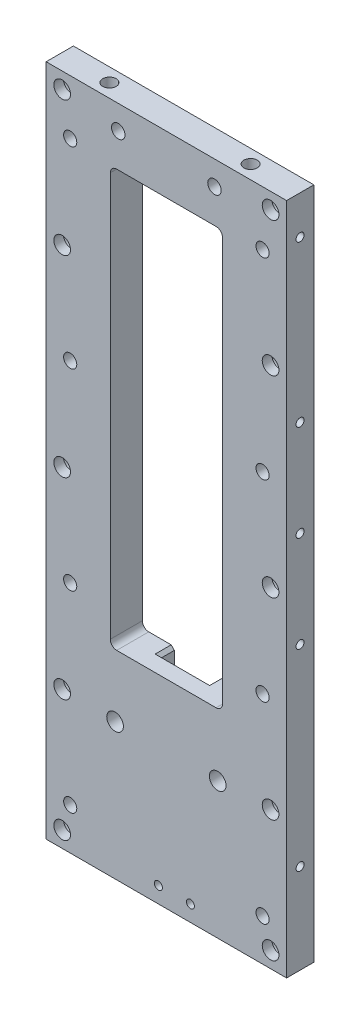
SolidWorks part; units mm, degrees
ref_plane "Front Plane" through (0, 0, 0) normal (0, 0, 1) x (1, 0, 0)
ref_plane "Top Plane" through (0, 0, 0) normal (0, 1, 0) x (1, 0, 0)
ref_plane "Right Plane" through (0, 0, 0) normal (1, 0, 0) x (0, 0, -1)
sketch "Sketch1" plane through (0, 0, 0) normal (0, 0, 1) x (1, 0, 0)
  line L0 (0, 0) -> (0, 230.9156) construction
  line L1 (0, 0) -> (0, -61.2047) construction
  line L2 (-37.5, 0) -> (0, 0)
  line L3 (0, 0) -> (37.5, 0)
  line L4 (-37.5, 210) -> (0, 210)
  line L5 (0, 210) -> (37.5, 210)
  line L6 (37.5, 210) -> (37.5, 0)
  line L7 (-37.5, 210) -> (-37.5, 0)
  point P8 (0, 230.9156)
  point P10 (0, 0)
  point P11 (0, 0)
  dimension "D1" = 75
  dimension "D2" = 210
extrude "Boss-Extrude1" add sketch "Sketch1" along normal blind 10
sketch "Sketch2" plane through (0, 0, 0) normal (0, 0, -1) x (-1, 0, 0)
  line L0 (0, 0) -> (0, 210) construction
  line L1 (-37.5, 210) -> (37.5, 210) construction
  line L2 (-30, 210) -> (-30, 0) construction
  line L3 (37.5, 0) -> (-37.5, 0) construction
  line L4 (-30, 193) -> (-18.2699, 193) construction
  line L5 (-30, 133) -> (-18.2699, 133) construction
  line L6 (-30, 73) -> (-18.2699, 73) construction
  line L7 (-30, 13) -> (-18.2699, 13) construction
  line L8 (-37.5, 0) -> (-37.5, 210) construction
  point P17 (0, 0)
  point P18 (0, 0)
  point P19 (0, 0)
  point P20 (0, 0)
  point P21 (30, 13)
  point P22 (30, 73)
  point P23 (30, 133)
  point P24 (30, 193)
  dimension "D1" = 30
  dimension "D2" = 60
  dimension "D3" = 60
  dimension "D4" = 60
  dimension "D5" = 17
hole_wizard "M5 Tapped Hole1" positions "3DSketch1" profile "Sketch3" tap size "M5" standard "GB"
sketch3d "3DSketch1"
  point P0 (30, 193, 0)
  point P3 (30, 133, 0)
  point P6 (30, 73, 0)
  point P9 (30, 13, 0)
  point P12 (-30, 13, 0)
  point P15 (-30, 73, 0)
  point P18 (-30, 133, 0)
  point P21 (-30, 193, 0)
sketch "Sketch3" plane through (30, 193, 0) normal (1, 0, 0) x (0, 1, 0)
  line L0 (0, 0) -> (0, 15.2318)
  line L1 (0, 15.2318) -> (2.05, 14)
  line L2 (2.05, 14) -> (2.05, 0)
  line L5 (2.05, 0) -> (0, 0)
  line L10 (0, 15.2318) -> (-2.05, 14) construction
  line L11 (0, -6.35) -> (0, 107.95) construction
  dimension "Tap Drill Dia." = 4.1
  dimension "Tap Drill Depth" = 14
  dimension "Drill Angle" = 118
cosmetic thread "Hole Thread1" parameters "D1"=10, "D2"=5
cosmetic thread "Hole Thread2" parameters "D1"=10, "D2"=5
cosmetic thread "Hole Thread3" parameters "D1"=10, "D2"=5
cosmetic thread "Hole Thread4" parameters "D1"=10, "D2"=5
cosmetic thread "Hole Thread5" parameters "D1"=10, "D2"=5
cosmetic thread "Hole Thread6" parameters "D1"=10, "D2"=5
cosmetic thread "Hole Thread7" parameters "D1"=10, "D2"=5
cosmetic thread "Hole Thread8" parameters "D1"=10, "D2"=5
sketch "Sketch4" plane through (0, 0, 0) normal (0, 0, -1) x (-1, 0, 0)
  line L0 (0, 0) -> (0, 210) construction
  line L1 (-37.5, 210) -> (37.5, 210) construction
  line L3 (17.5, 62) -> (-17.5, 62)
  line L4 (17.5, 62) -> (17.5, 192)
  line L5 (17.5, 192) -> (-17.5, 192)
  line L6 (-17.5, 62) -> (-17.5, 192)
  line L7 (17.5, 62) -> (-17.5, 192) construction
  line L8 (17.5, 192) -> (-17.5, 62) construction
  point P5 (0, 127)
  dimension "D1" = 127
  dimension "D2" = 130
  dimension "D3" = 35
extrude "Cut-Extrude1" cut sketch "Sketch4" against normal up to next
fillet "Fillet1" radius 2 4 edges at (17.5, 62, 5) (-17.5, 62, 5) (17.5, 192, 5) (-17.5, 192, 5)
sketch "Sketch6" plane through (0, 0, 0) normal (0, 0, -1) x (-1, 0, 0)
  line L0 (0, 0) -> (0, 210) construction
  line L1 (-37.5, 210) -> (37.5, 210) construction
  line L2 (-37.5, 210) -> (-37.5, 0)
  line L3 (-37.5, 0) -> (-22.5, 0)
  line L4 (37.5, 0) -> (-37.5, 0) construction
  line L5 (-22.5, 0) -> (-22.5, 210)
  line L6 (-22.5, 210) -> (-37.5, 210)
  line L7 (22.5, 0) -> (22.5, 210)
  line L8 (37.5, 0) -> (22.5, 0)
  line L9 (37.5, 210) -> (37.5, 0)
  line L10 (22.5, 210) -> (37.5, 210)
  dimension "D1" = 15
extrude "Cut-Extrude2" cut sketch "Sketch6" against normal blind 1.5
sketch "Sketch7" plane through (0, 0, 0) normal (0, 0, -1) x (-1, 0, 0)
  line L0 (-22.5, 210) -> (-22.5, 195)
  line L1 (-22.5, 0) -> (-22.5, 210) construction
  line L2 (-22.5, 195) -> (22.5, 195)
  line L3 (22.5, 210) -> (22.5, 0) construction
  line L4 (22.5, 195) -> (22.5, 210)
  line L5 (22.5, 210) -> (-22.5, 210)
  line L6 (15.5, 192) -> (-15.5, 192) construction
  dimension "D1" = 3
extrude "Cut-Extrude3" cut sketch "Sketch7" against normal blind 1.5
sketch "Sketch8" plane through (0, 0, 1.5) normal (0, 0, -1) x (-1, 0, 0)
  line L0 (0, 0) -> (0, 268.5028) construction
  line L1 (-32.5, 210) -> (-32.5, 0) construction
  line L2 (37.5, 210) -> (-37.5, 210) construction
  line L3 (-37.5, 0) -> (-22.5, 0) construction
  line L4 (-37.5, 210) -> (-37.5, 0) construction
  line L5 (-32.5, 205) -> (-27.8232, 205) construction
  line L6 (-32.5, 163) -> (-27.2642, 163) construction
  line L7 (-32.5, 103) -> (-27.2642, 103) construction
  line L8 (-32.5, 43) -> (-25.9311, 43) construction
  line L9 (-32.5, 5) -> (-27.2642, 5) construction
  point P24 (32.5, 5)
  point P25 (32.5, 43)
  point P26 (32.5, 103)
  point P27 (32.5, 163)
  point P28 (32.5, 205)
  dimension "D1" = 5
  dimension "D2" = 5
  dimension "D3" = 30
  dimension "D4" = 30
  dimension "D5" = 30
  dimension "D6" = 5
hole_wizard "CBORE for M5 Hex Socket Head Cap Screw1" positions "3DSketch2" profile "Sketch9" counterbore size "M5" standard "ISO" end condition through all
sketch3d "3DSketch2"
  point P0 (32.5, 205, 1.5)
  point P3 (32.5, 163, 1.5)
  point P6 (32.5, 103, 1.5)
  point P9 (32.5, 43, 1.5)
  point P12 (32.5, 5, 1.5)
  point P15 (-32.5, 5, 1.5)
  point P18 (-32.5, 43, 1.5)
  point P21 (-32.5, 103, 1.5)
  point P24 (-32.5, 163, 1.5)
  point P27 (-32.5, 205, 1.5)
sketch "Sketch9" plane through (32.5, 205, 1.5) normal (1, 0, 0) x (0, 1, 0)
  line L0 (0, 0) -> (0, 8.5)
  line L1 (0, 8.5) -> (2.6, 8.5)
  line L3 (2.6, 8.5) -> (2.6, 5.5)
  line L4 (2.6, 5.5) -> (4.25, 5.5)
  line L5 (4.25, 5.5) -> (4.25, 0)
  line L7 (4.25, 0) -> (0, 0)
  line L11 (0, -6.35) -> (0, 107.95) construction
  dimension "Thru Hole Dia." = 5.2
  dimension "Thru Hole Depth" = 8.5
  dimension "C'Bore Dia." = 8.5
  dimension "C'Bore Depth" = 5.5
sketch "Sketch10" plane through (0, 210, 0) normal (0, 1, 0) x (1, 0, 0)
  line L0 (0, 0) -> (0, -10) construction
  line L1 (37.5, -10) -> (-37.5, -10) construction
  line L4 (-22, -5.75) -> (-22, -10) construction
  point P5 (22, -5.75)
  dimension "D1" = 22
  dimension "D2" = 4.25
hole_wizard "M5 Tapped Hole2" positions "3DSketch3" profile "Sketch11" tap size "M5" standard "GB"
sketch3d "3DSketch3"
  point P0 (-22, 210, 5.75)
  point P3 (22, 210, 5.75)
sketch "Sketch11" plane through (-22, 210, 5.75) normal (1, 0, 0) x (0, 0, 1)
  line L0 (0, 0) -> (0, 17.2618)
  line L1 (0, 17.2618) -> (2.1, 16)
  line L2 (2.1, 16) -> (2.1, 0)
  line L5 (2.1, 0) -> (0, 0)
  line L10 (0, 17.2618) -> (-2.1, 16) construction
  line L11 (0, -6.35) -> (0, 107.95) construction
  dimension "Tap Drill Dia." = 4.2
  dimension "Tap Drill Depth" = 16
  dimension "Drill Angle" = 118
cosmetic thread "Hole Thread9" parameters "D1"=12, "D2"=5
cosmetic thread "Hole Thread10" parameters "D1"=12, "D2"=5
sketch "Sketch12" plane through (0, 0, 1.5) normal (0, 0, -1) x (-1, 0, 0)
  line L0 (0, 0) -> (0, 210) construction
  line L1 (37.5, 210) -> (-37.5, 210) construction
  line L2 (-18.6459, 202.5) -> (-15, 202.5) construction
  line L3 (-15, 207.873) -> (-15, 202.5) construction
  line L4 (-22.5, 195) -> (22.5, 195) construction
  point P10 (15, 202.5)
  dimension "D1" = 15
  dimension "D2" = 7.5
hole_wizard "M5 Tapped Hole3" positions "3DSketch4" profile "Sketch13" tap size "M5" standard "GB"
sketch3d "3DSketch4"
  point P0 (15, 202.5, 1.5)
  point P3 (-15, 202.5, 1.5)
sketch "Sketch13" plane through (15, 202.5, 1.5) normal (1, 0, 0) x (0, 1, 0)
  line L0 (0, 0) -> (0, 104.8218)
  line L1 (0, 104.8218) -> (2.1, 103.56)
  line L2 (2.1, 103.56) -> (2.1, 0)
  line L5 (2.1, 0) -> (0, 0)
  line L10 (0, 104.8218) -> (-2.1, 103.56) construction
  line L11 (0, -6.35) -> (0, 107.95) construction
  dimension "Tap Drill Dia." = 4.2
  dimension "Tap Drill Depth" = 103.56
  dimension "Drill Angle" = 118
cosmetic thread "Hole Thread11" parameters "D1"=8.5, "D2"=5
cosmetic thread "Hole Thread12" parameters "D1"=8.5, "D2"=5
sketch "Sketch14" plane through (0, 0, 0) normal (0, 0, -1) x (-1, 0, 0)
  line L0 (-22.5, 53) -> (22.5, 53)
  line L1 (-22.5, 0) -> (-22.5, 195) construction
  line L2 (22.5, 195) -> (22.5, 0) construction
  line L3 (22.5, 53) -> (22.5, 35)
  line L4 (22.5, 195) -> (22.5, 0) construction
  line L5 (22.5, 35) -> (-22.5, 35)
  line L6 (-22.5, 35) -> (-22.5, 53)
  line L7 (-15.5, 62) -> (15.5, 62) construction
  dimension "D1" = 27
  dimension "D2" = 18
extrude "Cut-Extrude4" cut sketch "Sketch14" against normal blind 5
fillet "Fillet2" radius 2 4 edges at (-22.5, 35, 3.25) (22.5, 35, 3.25) (-22.5, 53, 3.25) (22.5, 53, 3.25)
sketch "Sketch15" plane through (0, 0, 0) normal (0, 0, -1) x (-1, 0, 0)
  line L0 (0, 0) -> (0, 78.6156) construction
  line L1 (-15.5, 62) -> (15.5, 62) construction
  line L2 (-7.5, 53) -> (7.5, 53)
  line L3 (-7.5, 53) -> (-7.5, 71)
  line L4 (-7.5, 71) -> (7.5, 71)
  line L5 (7.5, 53) -> (7.5, 71)
  line L6 (-7.5, 53) -> (7.5, 71) construction
  line L7 (-7.5, 71) -> (7.5, 53) construction
  line L8 (20.5, 53) -> (-20.5, 53) construction
  point P3 (0, 62)
  point P10 (0, 0)
  dimension "D1" = 15
extrude "Cut-Extrude6" cut sketch "Sketch15" against normal up to surface (5 mm away) up to face at (0, 44, 5)
sketch "Sketch16" plane through (0, 0, 5) normal (0, 0, -1) x (-1, 0, 0)
  line L0 (0, 0) -> (0, 54.4041) construction
  line L1 (-16, 47.782) -> (-16, 42.5) construction
  line L2 (-16, 42.5) -> (-9.3094, 42.5) construction
  line L3 (22.5, 0) -> (-22.5, 0) construction
  point P6 (0, 0)
  point P9 (16, 42.5)
  dimension "D1" = 16
  dimension "D2" = 42.5
hole_wizard "Tap Drill for M5 Tap1" positions "3DSketch5" profile "Sketch17" hole size "M5" standard "GB"
sketch3d "3DSketch5"
  point P0 (16, 42.5, 5)
  point P3 (-16, 42.5, 5)
sketch "Sketch17" plane through (16, 42.5, 5) normal (1, 0, 0) x (0, 1, 0)
  line L0 (0, 0) -> (0, 47.5622)
  line L1 (0, 47.5622) -> (2.6, 46)
  line L2 (2.6, 46) -> (2.6, 0.4)
  line L3 (2.6, 0.4) -> (3, 0)
  line L5 (3, 0) -> (0, 0)
  line L6 (-2.6, 0.4) -> (-3, 0) construction
  line L10 (0, 47.5622) -> (-2.6, 46) construction
  line L11 (0, -6.35) -> (0, 107.95) construction
  dimension "Hole Dia." = 5.2
  dimension "Hole Depth" = 46
  dimension "Near C'Sink Dia." = 6
  dimension "Near C'Sink Angle" = 90
  dimension "Drill Angle" = 118
chamfer "Chamfer1" distance 1 angle 45 10 edges at (22.5, 195, 0.75) (-22.5, 195, 0.75) (-7.5, 53, 2.5) (-7.5, 62, 2.5) (7.5, 62, 2.5) (7.5, 53, 2.5) (-22.5, 53, 0.75) (22.5, 53, 0.75) (-22.5, 35, 0.75) (22.5, 35, 0.75)
sketch "Sketch19" plane through (-37.5, 0, 0) normal (-1, 0, 0) x (0, 0, 1)
  line L0 (5.8, 210) -> (5.8, 0) construction
  line L1 (10, 210) -> (1.5, 210) construction
  line L2 (10, 0) -> (1.5, 0) construction
  line L3 (10, 210) -> (10, 0) construction
  line L4 (5.8, 198) -> (8.2767, 198) construction
  line L5 (5.8, 148) -> (8.2767, 148) construction
  line L6 (5.8, 118) -> (7.7239, 118) construction
  line L7 (5.8, 88) -> (8.2767, 88) construction
  line L8 (5.8, 28) -> (8.2767, 28) construction
  dimension "D1" = 4.2
  dimension "D2" = 12
  dimension "D3" = 50
  dimension "D4" = 30
  dimension "D5" = 30
  dimension "D6" = 60
hole_wizard "M3 Tapped Hole1" positions "3DSketch6" profile "Sketch20" tap size "M3" standard "GB"
sketch3d "3DSketch6"
  point P0 (-37.5, 198, 5.8)
  point P3 (-37.5, 148, 5.8)
  point P6 (-37.5, 118, 5.8)
  point P9 (-37.5, 88, 5.8)
  point P12 (-37.5, 28, 5.8)
sketch "Sketch20" plane through (-37.5, 198, 5.8) normal (0, 1, 0) x (0, 0, 1)
  line L0 (0, 0) -> (0, 9.2511)
  line L1 (0, 9.2511) -> (1.25, 8.5)
  line L2 (1.25, 8.5) -> (1.25, 0)
  line L5 (1.25, 0) -> (0, 0)
  line L10 (0, 9.2511) -> (-1.25, 8.5) construction
  line L11 (0, -6.35) -> (0, 107.95) construction
  dimension "Tap Drill Dia." = 2.5
  dimension "Tap Drill Depth" = 8.5
  dimension "Drill Angle" = 118
cosmetic thread "Hole Thread13" parameters "D1"=6, "D2"=3
cosmetic thread "Hole Thread14" parameters "D1"=6, "D2"=3
cosmetic thread "Hole Thread15" parameters "D1"=6, "D2"=3
cosmetic thread "Hole Thread16" parameters "D1"=6, "D2"=3
cosmetic thread "Hole Thread17" parameters "D1"=6, "D2"=3
mirror "Mirror1" about plane through (0, 0, 0) normal (1, 0, 0) of "M3 Tapped Hole1"
cosmetic thread "Hole Thread18" parameters "D1"=6, "D2"=3
cosmetic thread "Hole Thread19" parameters "D1"=6, "D2"=3
cosmetic thread "Hole Thread20" parameters "D1"=6, "D2"=3
cosmetic thread "Hole Thread21" parameters "D1"=6, "D2"=3
cosmetic thread "Hole Thread22" parameters "D1"=6, "D2"=3
sketch "Sketch21" plane through (0, 0, 0) normal (0, 0, -1) x (-1, 0, 0)
  line L0 (-7.5, 8.4263) -> (-7.5, 5) construction
  line L1 (-7.5, 5) -> (2.5, 5) construction
  line L2 (-22.5, 0) -> (-22.5, 34) construction
  line L3 (22.5, 0) -> (-22.5, 0) construction
  point P5 (0, 0)
  point P8 (7.2524, 5)
  dimension "D1" = 15
  dimension "D2" = 5
  dimension "D3" = 10
hole_wizard "M3 Tapped Hole2" positions "3DSketch7" profile "Sketch22" tap size "M3" standard "GB" end condition through all
sketch3d "3DSketch7"
  point P0 (7.5, 5, 0)
  point P3 (-2.5, 5, 0)
sketch "Sketch22" plane through (7.5, 5, 0) normal (1, 0, 0) x (0, 1, 0)
  line L0 (0, 0) -> (0, 10)
  line L1 (0, 10) -> (1.25, 10)
  line L2 (1.25, 10) -> (1.25, 0)
  line L5 (1.25, 0) -> (0, 0)
  line L11 (0, -6.35) -> (0, 107.95) construction
  dimension "Thru Tap Drill Dia." = 2.5
  dimension "Thru Tap Drill Depth" = 10
cosmetic thread "Hole Thread23" parameters "D2"=3
cosmetic thread "Hole Thread24" parameters "D2"=3
